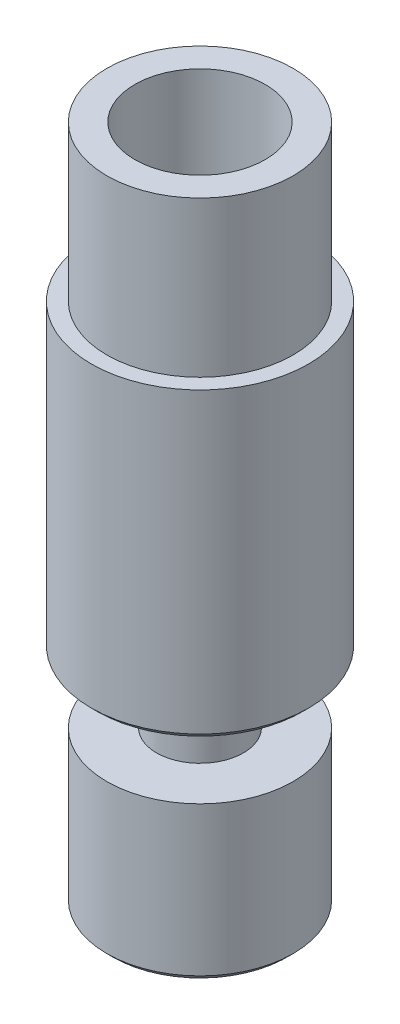
SolidWorks part; units mm, degrees
material "AISI 304"
ref_plane "Front Plane" through (0, 0, 0) normal (0, 0, 1) x (1, 0, 0)
ref_plane "Top Plane" through (0, 0, 0) normal (0, 1, 0) x (1, 0, 0)
ref_plane "Right Plane" through (0, 0, 0) normal (1, 0, 0) x (0, 0, -1)
sketch "Sketch1" plane through (0, 0, 0) normal (0, 0, 1) x (1, 0, 0)
  line L0 (1, -10.95) -> (1, 5.3149)
  line L1 (0, 10.95) -> (0, -10.95) construction
  line L2 (1, 5.3149) -> (2.1, 5.95)
  line L3 (2.1, 5.95) -> (2.1, 10.95)
  line L4 (2.1, 10.95) -> (3, 10.95)
  line L6 (3, 10.95) -> (3, 5.95)
  line L7 (3, 5.95) -> (3.5, 5.95)
  line L8 (3.5, 5.95) -> (3.5, -3.85)
  line L9 (3.5, -3.85) -> (1.4, -3.85)
  line L10 (1.4, -3.85) -> (1.4, -5.95)
  line L11 (1.4, -5.95) -> (3, -5.95)
  line L12 (3, -5.95) -> (3, -10.95)
  line L14 (3, -10.95) -> (1, -10.95)
  dimension "D1" = 21.9
  dimension "D2" = 2
  dimension "D3" = 4.2
  dimension "D5" = 6
  dimension "D6" = 7
  dimension "D7" = 6
  dimension "D8" = 7.1
  dimension "D9" = 2.1
  dimension "D10" = 5
  dimension "D11" = 120
  dimension "D12" = 2.8
revolve "Revolve1" add sketch "Sketch1" angle 360 about L1
cosmetic thread "Cosmetic Thread1"
cosmetic thread "Cosmetic Thread2"
chamfer "Chamfer1" distance 0.2 angle 45 3 edges at (0, -10.95, 1) (0, -10.95, 3) (0, -3.85, 3.5)
